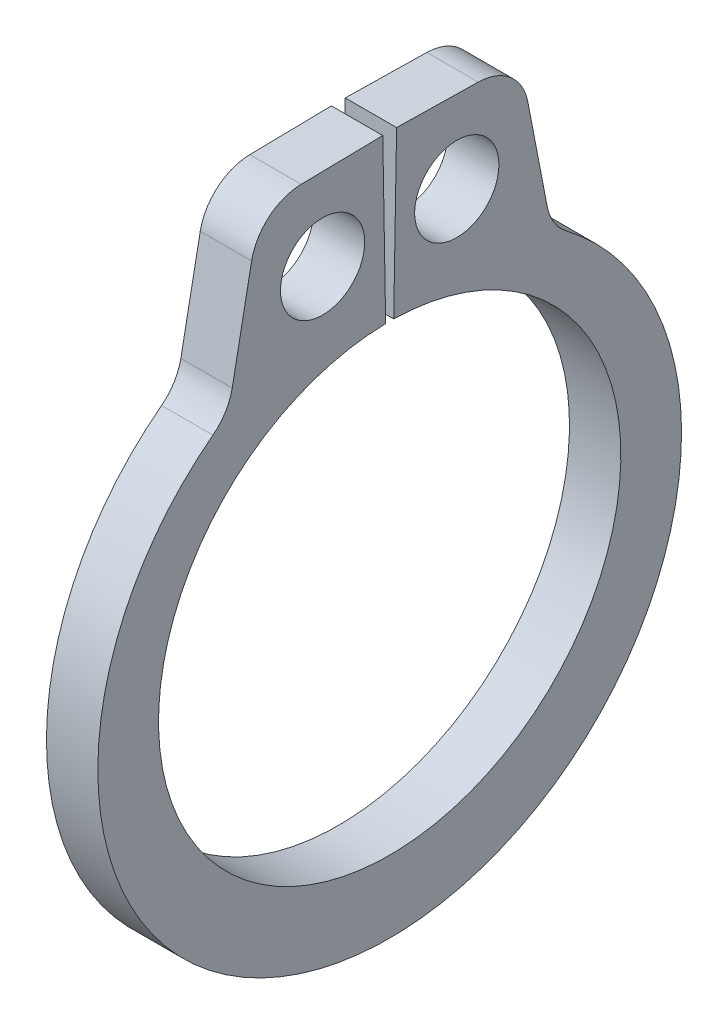
SolidWorks part; units mm, degrees
material "Cast Carbon Steel"
ref_plane "Front" through (0, 0, 0) normal (0, 0, 1) x (1, 0, 0)
ref_plane "Top" through (0, 0, 0) normal (0, 1, 0) x (1, 0, 0)
ref_plane "Right" through (0, 0, 0) normal (1, 0, 0) x (0, 0, -1)
sketch "Sketch1" plane through (0, 0, 0) normal (1, 0, 0) x (0, 0, -1)
  line L0 (0, 0) -> (0, 2.8575) construction
  line L1 (-0.0499, 2.8571) -> (-0.0853, 4.8888)
  line L2 (0.0853, 4.8888) -> (1.6091, 4.8622)
  line L3 (1.6091, 4.8622) -> (1.9944, 2.867)
  line L4 (0.0499, 2.8571) -> (0.0853, 4.8888)
  line L5 (-0.0853, 4.8888) -> (-1.6091, 4.8622)
  line L6 (-1.6091, 4.8622) -> (-1.9944, 2.867)
  line L7 (-1.9944, 2.867) -> (-1.6318, 2.3457) construction
  line L8 (1.9944, 2.867) -> (1.6318, 2.3457) construction
  line L9 (0, -2.8575) -> (0, -3.7465) construction
  line L10 (-1.6091, 4.8622) -> (-0.0499, 2.8571) construction
  line L11 (0, 2.8575) -> (0, 4.8895) construction
  line L12 (-2.8575, 0) -> (2.8575, 0) construction
  circle A0 centre (0, 0) radius 2.8575 construction
  arc A1 (-0.0499, 2.8571) -> (0.0499, 2.8571) centre (0, 0) ccw
  circle A3 centre (0, 0) radius 5.588 construction
  circle A4 centre (-0.8295, 3.8596) radius 0.5207
  circle A5 centre (0.8295, 3.8596) radius 0.5207
  arc A6 (-1.9944, 2.867) -> (1.9944, 2.867) centre (0, -0.139) ccw
  point P0 (0, -3.7465)
  dimension "A" = 5.715
  dimension "D2" = 1.524
  dimension "L" = 11.176
  dimension "Hole" = 1.0414
  dimension "Smin" = 0.635
  dimension "Smax" = 0.889
  dimension "H" = 2.032
  dimension "Angle" = 1
extrude "Extrude1" add sketch "Sketch1" along normal mid plane 0.635
fillet "Fillet1" radius 0.635 4 edges at (0, 2.867, 1.9944) (0, 2.867, -1.9944) (0, 4.8622, 1.6091) (0, 4.8622, -1.6091)
sketch "Sketch2" plane through (0, 0, 0) normal (0, 0, 1) x (1, 0, 0)
  line L0 (-3.5433, 0) -> (9.1567, 0)
  line L1 (9.1567, 0) -> (9.1567, -3.175)
  line L2 (-0.3683, -3.175) -> (-3.2893, -3.175)
  line L3 (9.1567, -3.175) -> (0.3683, -3.175)
  line L4 (0.3683, -3.175) -> (0.3683, -2.921)
  line L5 (0.3683, -2.921) -> (-0.3683, -2.921)
  line L6 (-0.3683, -2.921) -> (-0.3683, -3.175)
  line L7 (-0.3683, -3.175) -> (-3.5433, -3.175) construction
  line L8 (-3.5433, -3.175) -> (-3.5433, 0) construction
  line L9 (9.1567, 0) -> (76.391, 0) construction
  line L10 (-3.2893, -3.175) -> (-3.5433, -2.921)
  line L11 (-3.5433, -2.921) -> (-3.5433, 0)
  point P10 (0, -2.921)
  dimension "D1" = 45
  dimension "Dg" = 5.842
  dimension "Ds" = 6.35
  dimension "W" = 0.7366
  dimension "D2" = 12.7
  dimension "D3" = 3.175
revolve "Revolve1" [suppressed] add sketch "Sketch2" angle 360 about L9
delete or keep bodies "Body-Delete1" [suppressed] type delete bodies bodies 122
equation "\"D2@Sketch2\" = \"D1@Extrude1\"*20"
equation "\"D3@Sketch2\" = \"D2@Sketch2\"/4"
equation "\"D2@Sketch1\" = \"H@Sketch1\"*.75"
